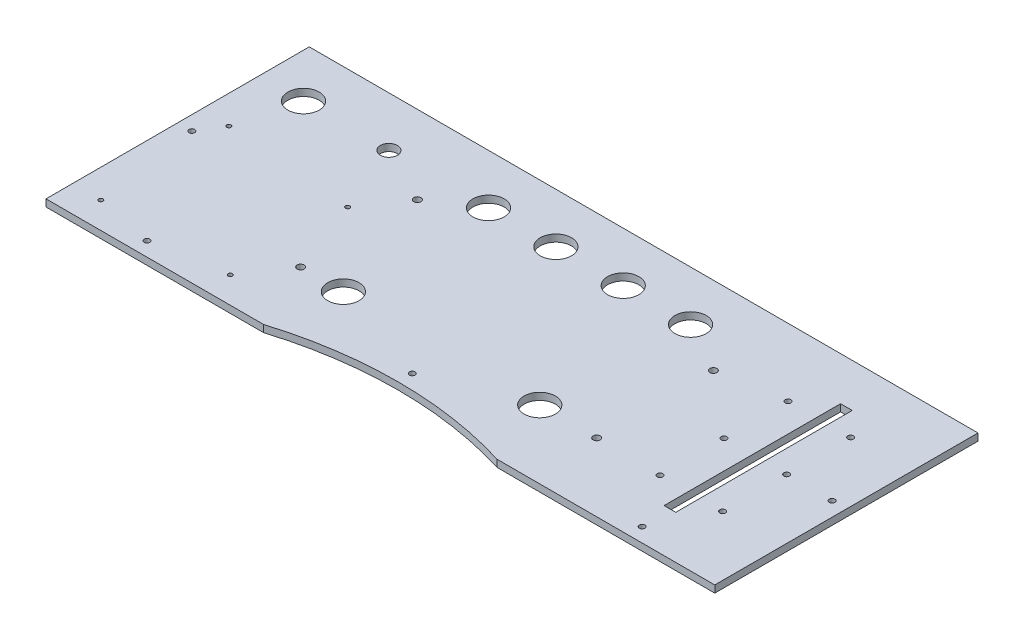
SolidWorks part; units mm, degrees
ref_plane "前视基准面" through (0, 0, 0) normal (0, 0, 1) x (1, 0, 0)
ref_plane "上视基准面" through (0, 0, 0) normal (0, 1, 0) x (1, 0, 0)
ref_plane "右视基准面" through (0, 0, 0) normal (1, 0, 0) x (0, 0, -1)
sketch "草图1" plane through (0, 0, 0) normal (0, 1, 0) x (1, 0, 0)
  line L0 (-104, 92.5) -> (-104, -92.5) construction
  line L1 (-235, 92.5) -> (235, 92.5)
  line L2 (-235, 92.5) -> (-235, -92.5)
  line L3 (-235, -92.5) -> (-104, -92.5)
  line L4 (235, 92.5) -> (235, -92.5)
  line L5 (104, 92.5) -> (104, -92.5) construction
  line L6 (-235, 0) -> (235, 0) construction
  line L7 (168.9, 62) -> (177.1, 62)
  line L8 (168.9, 62) -> (168.9, -62)
  line L9 (168.9, -62) -> (177.1, -62)
  line L10 (177.1, 62) -> (177.1, -62)
  line L11 (173, 62) -> (173, -62) construction
  line L12 (0, 92.5) -> (0, -80.102) construction
  line L13 (104, -92.5) -> (235, -92.5)
  line L14 (-104, -92.5) -> (-82, -92.5)
  line L15 (-82, 92.5) -> (-82, -92.5) construction
  line L16 (82, 92.5) -> (82, -92.5) construction
  line L17 (82, -92.5) -> (104, -92.5)
  circle A0 centre (-104, 37.5) radius 2.5
  circle A1 centre (-104, -44.5) radius 2.5
  circle A2 centre (104, 37.5) radius 2.5
  circle A3 centre (104, -44.5) radius 2.5
  circle A4 centre (-74, 57.5) radius 11
  circle A5 centre (-26.67, 57.5) radius 11
  circle A6 centre (20.67, 57.5) radius 11
  circle A7 centre (68, 57.5) radius 11
  circle A8 centre (64, -44.5) radius 11
  circle A9 centre (-204, 57.5) radius 11
  circle A10 centre (-74, -44.5) radius 11
  circle A11 centre (149, 0) radius 2
  circle A12 centre (193, 0) radius 2
  circle A13 centre (149, 45) radius 2
  circle A14 centre (149, -45) radius 2
  circle A15 centre (193, 45) radius 2
  circle A16 centre (193, -45) radius 2
  circle A17 centre (-124, -74) radius 1.5
  circle A18 centre (-124, 8.5) radius 1.5
  circle A19 centre (-215, -74) radius 1.5
  circle A20 centre (-215, 16) radius 1.5
  circle A21 centre (-144, 57.5) radius 6
  circle A23 centre (0, -70.102) radius 2
  circle A24 centre (-174, -82.5) radius 2
  circle A25 centre (174, -82.5) radius 2
  circle A26 centre (-225, 0) radius 2
  circle A27 centre (225, 0) radius 2
  arc A28 (-82, -92.5) -> (82, -92.5) centre (0, -358.5793) cw
  dimension "D7" = 5
  dimension "D8" = 5
  dimension "D11" = 5
  dimension "D12" = 5
  dimension "D15" = 22
  dimension "D21" = 22
  dimension "D22" = 22
  dimension "D23" = 22
  dimension "D24" = 22
  dimension "D28" = 22
  dimension "D30" = 22
  dimension "D34" = 4
  dimension "D35" = 4
  dimension "D41" = 4
  dimension "D42" = 4
  dimension "D43" = 4
  dimension "D44" = 4
  dimension "D50" = 3
  dimension "D51" = 3
  dimension "D53" = 3
  dimension "D55" = 3
  dimension "D58" = 12
  dimension "D59" = 22
  dimension "D60" = 4
  dimension "D61" = 10
  dimension "D62" = 4
  dimension "D63" = 10
  dimension "D65" = 4
  dimension "D68" = 4
  dimension "D70" = 4
  dimension "D71" = 10
  dimension "D1" = 470
  dimension "D2" = 235
  dimension "D3" = 185
  dimension "D4" = 92.5
  dimension "D5" = 104
  dimension "D6" = 104
  dimension "D9" = 55
  dimension "D10" = 48
  dimension "D13" = 55
  dimension "D14" = 48
  dimension "D16" = 35
  dimension "D17" = 30
  dimension "D18" = 36
  dimension "D19" = 47.33
  dimension "D20" = 47.33
  dimension "D25" = 40
  dimension "D26" = 35
  dimension "D27" = 35
  dimension "D29" = 100
  dimension "D31" = 8.2
  dimension "D32" = 62
  dimension "D33" = 62
  dimension "D36" = 24
  dimension "D37" = 20
  dimension "D38" = 45
  dimension "D39" = 45
  dimension "D40" = 45
  dimension "D45" = 45
  dimension "D46" = 45
  dimension "D47" = 84
  dimension "D48" = 20
  dimension "D49" = 20
  dimension "D52" = 82.5
  dimension "D54" = 91
  dimension "D56" = 90
  dimension "D57" = 60
  dimension "D64" = 70
  dimension "D66" = 10
  dimension "D67" = 70
  dimension "D69" = 10
  dimension "D72" = 22
extrude "凸台-拉伸1" add sketch "草图1" along normal blind 5
